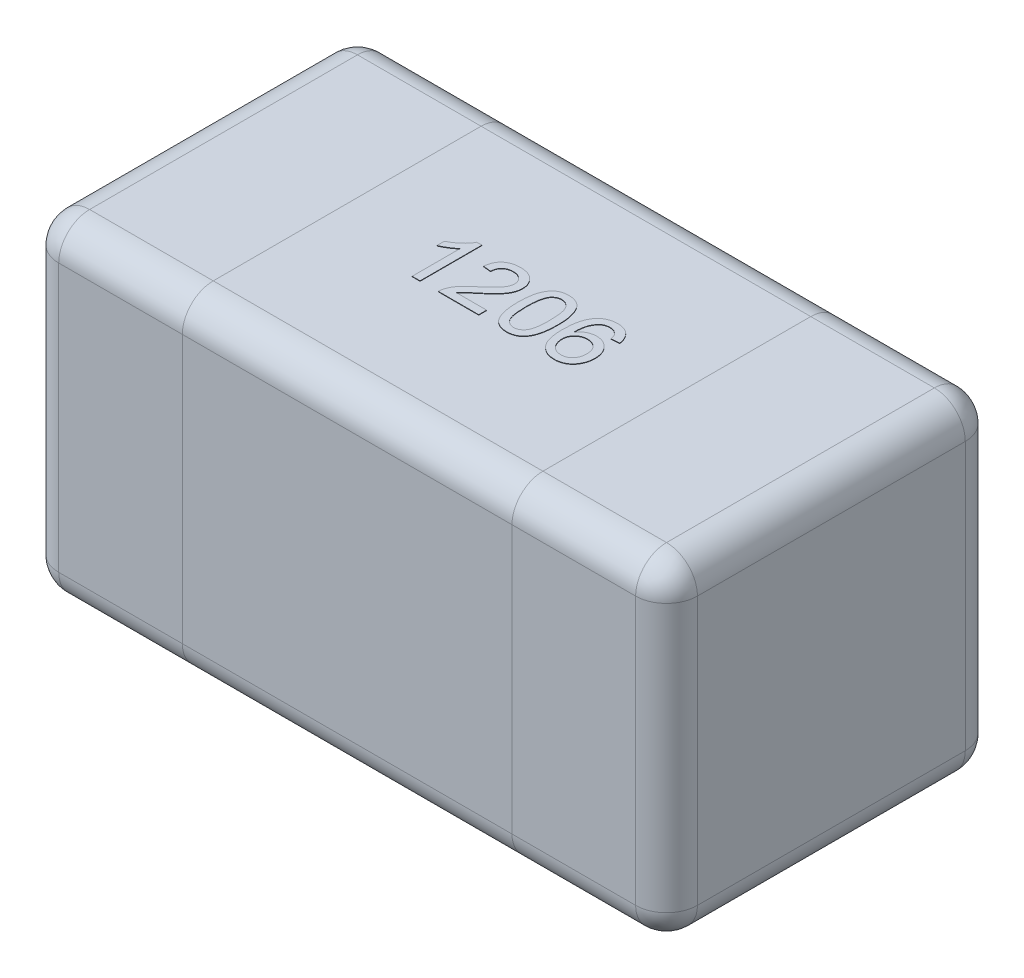
SolidWorks part; units mm, degrees
ref_plane "Front" through (0, 0, 0) normal (0, 0, 1) x (1, 0, 0)
ref_plane "Top" through (0, 0, 0) normal (0, 1, 0) x (1, 0, 0)
ref_plane "Right" through (0, 0, 0) normal (1, 0, 0) x (0, 0, -1)
sketch "Sketch1" plane through (0, 0, 0) normal (0, 1, 0) x (1, 0, 0)
  line L0 (0, -5.3126) -> (0, 5.729) construction
  line L1 (-6.1479, 0) -> (7.7291, 0) construction
  line L3 (-1.55, 0.8) -> (1.55, 0.8)
  line L4 (-1.55, 0.8) -> (-1.55, -0.8)
  line L5 (-1.55, -0.8) -> (1.55, -0.8)
  line L6 (1.55, 0.8) -> (1.55, -0.8)
  dimension "D1" = 3.1
  dimension "D2" = 1.6
extrude "Extrude1" add sketch "Sketch1" along normal blind 1.6
fillet "Fillet1" radius 0.15 12 edges at (0, 1.6, 0.8) (-1.55, 0.8, -0.8) (0, 0, -0.8) (-1.55, 0, 0) (-1.55, 0.8, 0.8) (0, 0, 0.8) (1.55, 0.8, 0.8) (1.55, 0.8, -0.8) (1.55, 0, 0) (0, 1.6, -0.8) (1.55, 1.6, 0) (-1.55, 1.6, 0)
sketch "Sketch2" plane through (0, 0, 0.8) normal (0, 0, 1) x (1, 0, 0)
  line L0 (-1.4, 1.6) -> (1.4, 1.6) construction
  line L1 (-0.8, 1.6) -> (0.8, 1.6)
  line L2 (-0.8, 1.6) -> (-0.8, 0)
  line L3 (-0.8, 0) -> (0.8, 0)
  line L4 (0.8, 1.6) -> (0.8, 0)
  line L5 (1.4, 0) -> (-1.4, 0) construction
  line L6 (-1.55, 0.15) -> (-1.55, 1.45) construction
  line L7 (0, -0.2963) -> (0, 3.0124) construction
  dimension "D1" = 0.75
split line "Split Line1"
sketch "Sketch3" plane through (0, 1.6, 0) normal (0, 1, 0) x (1, 0, 0)
  text T0 "1206" font "Arial" height 0.3
  dimension "D1" = 0.45
  dimension "D2" = 0.15
extrude "Extrude2" add sketch "Sketch3" along normal blind 0.002
